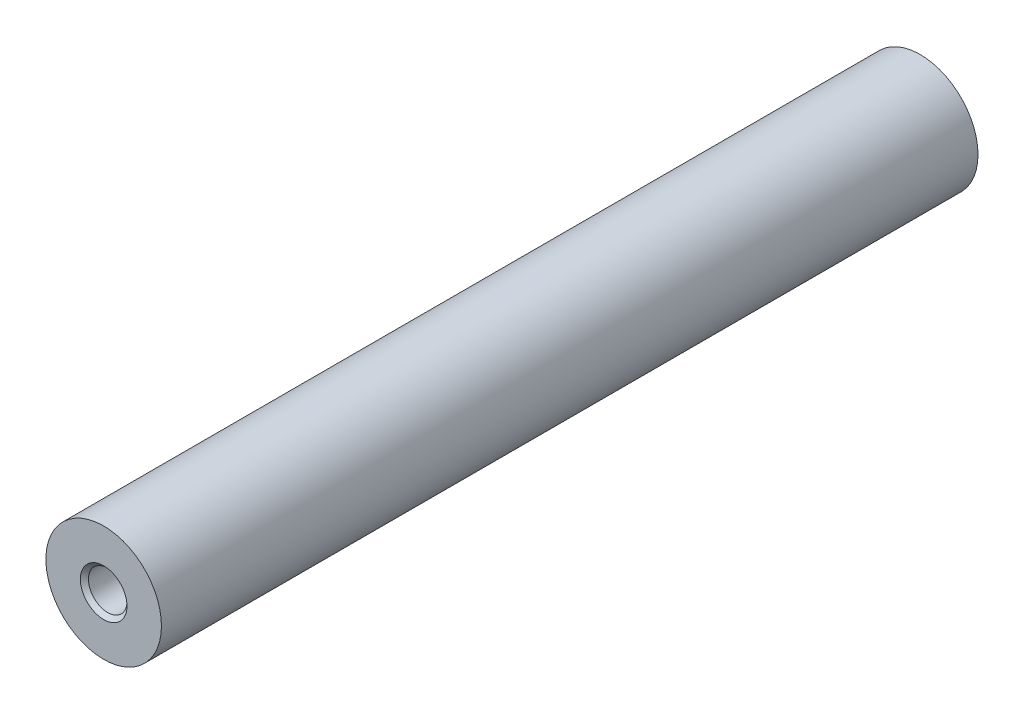
SolidWorks part; units mm, degrees
ref_plane "Front Plane" through (0, 0, 0) normal (0, 0, 1) x (1, 0, 0)
ref_plane "Top Plane" through (0, 0, 0) normal (0, 1, 0) x (1, 0, 0)
ref_plane "Right Plane" through (0, 0, 0) normal (1, 0, 0) x (0, 0, -1)
sketch "Sketch1" plane through (0, 0, 0) normal (0, 0, 1) x (1, 0, 0)
  circle A0 centre (0, 0) radius 7.5
  dimension "D1" = 15
extrude "Boss-Extrude1" add sketch "Sketch1" along normal mid plane 106
hole_wizard "M6x1.0 Tapped Hole1" positions "Sketch2" profile "Sketch3" tap size "M6x1.0" standard "ANSI Metric"
sketch "Sketch2" plane through (0, 0, 53) normal (0, 0, 1) x (1, 0, 0)
  point P0 (0, 0)
sketch "Sketch3" plane through (0, 0, 53) normal (1, 0, 0) x (0, -1, 0)
  line L0 (0, 0) -> (0, 16.5022)
  line L1 (0, 16.5022) -> (2.5, 15)
  line L2 (2.5, 15) -> (2.5, 0.525)
  line L3 (2.5, 0.525) -> (3.025, 0)
  line L5 (3.025, 0) -> (0, 0)
  line L6 (-2.5, 0.525) -> (-3.025, 0) construction
  line L10 (0, 16.5022) -> (-2.5, 15) construction
  line L11 (0, -6.35) -> (0, 107.95) construction
  dimension "Tap Drill Dia." = 5
  dimension "Tap Drill Depth" = 15
  dimension "Near C'Sink Dia." = 6.05
  dimension "Near C'Sink Angle" = 90
  dimension "Drill Angle" = 118
cosmetic thread "Hole Thread1" parameters "D1"=12, "D2"=6
mirror "Mirror1" about plane through (0, 0, 0) normal (0, 0, 1) of "M6x1.0 Tapped Hole1"
cosmetic thread "Hole Thread2"
